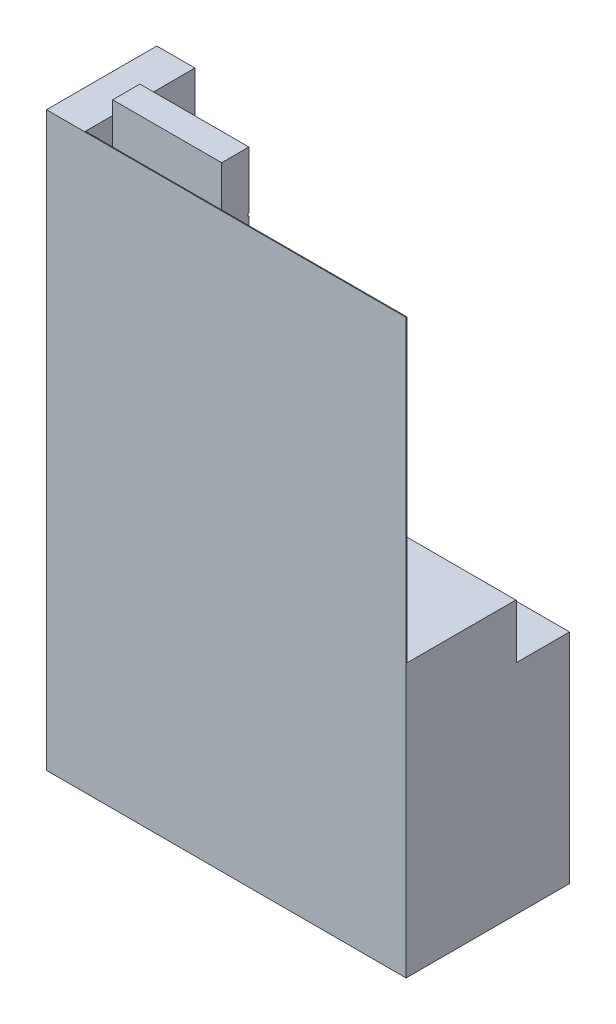
SolidWorks part; units mm, degrees
material "Balsa"
ref_plane "Front Plane" through (0, 0, 0) normal (0, 0, 1) x (1, 0, 0)
ref_plane "Top Plane" through (0, 0, 0) normal (0, 1, 0) x (1, 0, 0)
ref_plane "Right Plane" through (0, 0, 0) normal (1, 0, 0) x (0, 0, -1)
sketch "Sketch1" plane through (0, 0, 0) normal (0, 0, 1) x (1, 0, 0)
  line L1 (-600, 400) -> (600, 400)
  line L2 (-600, 400) -> (-600, -400)
  line L3 (-600, -400) -> (600, -400)
  line L4 (600, 400) -> (600, -400)
  line L5 (-600, 400) -> (600, -400) construction
  line L6 (-600, -400) -> (600, 400) construction
  point P0 (0, 0)
  dimension "D1" = 1200
  dimension "D2" = 800
extrude "Boss-Extrude1" add sketch "Sketch1" along normal blind 600
sketch "Sketch2" plane through (0, 0, 600) normal (0, 0, 1) x (1, 0, 0)
  line L0 (-600, -400) -> (600, -400) construction
  line L1 (600, 400) -> (-600, 400)
  line L2 (600, 400) -> (600, 1700)
  line L3 (600, 1700) -> (-600, 1700)
  line L4 (-600, 400) -> (-600, 1700)
  dimension "D1" = 2100
extrude "Boss-Extrude2" add sketch "Sketch2" against normal blind 3
sketch "Sketch5" plane through (0, 0, 597) normal (0, 0, -1) x (-1, 0, 0)
  line L0 (600, 1700) -> (600, 400) construction
  line L1 (600, 600) -> (-600, 600)
  line L2 (600, 600) -> (600, 590)
  line L3 (600, 590) -> (-600, 590)
  line L4 (-600, 600) -> (-600, 590)
  line L5 (600, 400) -> (-600, 400) construction
  dimension "D1" = 10
  dimension "D2" = 1200
  dimension "D3" = 190
extrude "Boss-Extrude6" add sketch "Sketch5" along normal blind 400
sketch "Sketch11" plane through (0, 0, 0) normal (1, 0, 0) x (0, 0, -1)
  line L0 (-197, 600) -> (0, 400)
rib "Rib1" sketch "Sketch11" sketch "Sketch11" thickness 1200 extrusion direction parallel to sketch draft on no parameters "D1"=1200
sketch "Sketch12" plane through (-600, 0, 0) normal (-1, 0, 0) x (0, 0, 1)
  line L0 (0, 400) -> (-7.2932, 406.8417)
  dimension "D1" = 10
extrude "Extrude-Thin1" add sketch "Sketch12" against normal up to surface (1200 mm away) thin
sketch "Sketch16" plane through (0, 0, 597) normal (0, 0, -1) x (-1, 0, 0)
  line L0 (600, 1700) -> (600, 600) construction
  line L1 (600, 927) -> (0, 927)
  line L2 (600, 927) -> (600, 917)
  line L3 (600, 917) -> (0, 917)
  line L4 (0, 927) -> (0, 917)
  line L5 (600, 600) -> (-600, 600) construction
  dimension "D1" = 317
  dimension "D2" = 10
  dimension "D3" = 600
extrude "Boss-Extrude11" add sketch "Sketch16" along normal blind 375
sketch "Sketch17" plane through (0, 0, 597) normal (0, 0, -1) x (-1, 0, 0)
  line L0 (600, 1700) -> (600, 927) construction
  line L1 (600, 1287) -> (0, 1287)
  line L2 (600, 1287) -> (600, 1277)
  line L3 (600, 1277) -> (0, 1277)
  line L4 (0, 1287) -> (0, 1277)
  line L5 (600, 927) -> (0, 927) construction
  dimension "D1" = 10
  dimension "D2" = 350
  dimension "D3" = 600
extrude "Boss-Extrude12" add sketch "Sketch17" along normal blind 375
sketch "Sketch18" plane through (0, 0, 597) normal (0, 0, -1) x (-1, 0, 0)
  line L1 (-513.7917, 1599.2738) -> (-63.7917, 1599.2738)
  line L2 (-513.7917, 1599.2738) -> (-513.7917, 849.2738)
  line L3 (-513.7917, 849.2738) -> (-63.7917, 849.2738)
  line L4 (-63.7917, 1599.2738) -> (-63.7917, 849.2738)
  dimension "D1" = 450
  dimension "D2" = 750
extrude "Boss-Extrude13" add sketch "Sketch18" along normal blind 40 separate body
sketch "Sketch21" plane through (0, 0, 557) normal (0, 0, -1) x (-1, 0, 0)
  line L0 (-513.7917, 1599.2738) -> (-513.7917, 849.2738) construction
  text T0 "Back Light" font "BodoniFLF" height in points 200
  point P3 (-513.7917, 1224.2738)
extrude "Cut-Extrude7" cut sketch "Sketch21" against normal blind 3
sketch "Sketch22" plane through (0, 0, 597) normal (0, 0, -1) x (-1, 0, 0)
  line L1 (100, 1850) -> (500, 1850)
  line L2 (100, 1850) -> (100, 1550)
  line L3 (100, 1550) -> (500, 1550)
  line L4 (500, 1850) -> (500, 1550)
  line L5 (-600, 1700) -> (600, 1700) construction
  line L6 (600, 1700) -> (600, 1287) construction
  point P6 (100, 1700)
  dimension "D1" = 400
  dimension "D2" = 300
  dimension "D3" = 100
extrude "Boss-Extrude15" add sketch "Sketch22" along normal blind 100 separate body
sketch "Sketch23" plane through (0, 0, 497) normal (0, 0, -1) x (-1, 0, 0)
  line L0 (100, 1850) -> (100, 1550) construction
  text T0 "ara" font "BodoniFLF" height in points 500
  text T1 "PERFUME" font "BodoniFLF" height in points 100
  point P3 (100, 1700)
  dimension "D1" = 60
  dimension "D2" = 80
  dimension "D3" = 47
extrude "Cut-Extrude10" cut sketch "Sketch23" against normal blind 3
sketch "Sketch24" plane through (0, 0, 497) normal (0, 0, -1) x (-1, 0, 0)
  line L0 (100, 1850) -> (100, 1550) construction
  line L1 (100, 1640) -> (185, 1640)
  line L2 (100, 1640) -> (100, 1630)
  line L3 (100, 1630) -> (185, 1630)
  line L4 (185, 1640) -> (185, 1630)
  line L5 (100, 1550) -> (500, 1550) construction
  line L6 (300, 1550) -> (300, 1609.9434) construction
  line L7 (500, 1630) -> (415, 1630)
  line L8 (415, 1640) -> (415, 1630)
  line L9 (500, 1640) -> (415, 1640)
  line L10 (500, 1640) -> (500, 1630)
  dimension "D1" = 85
  dimension "D2" = 80
  dimension "D3" = 10
extrude "Cut-Extrude11" cut sketch "Sketch24" against normal blind 3
sketch "Sketch27" plane through (0, 0, 600) normal (0, 0, 1) x (1, 0, 0)
  line L1 (-600, -400) -> (-740, -400)
  line L2 (-600, -400) -> (-600, 1700)
  line L3 (-600, 1700) -> (-740, 1700)
  line L4 (-740, -400) -> (-740, 1700)
  dimension "D1" = 140
extrude "Boss-Extrude17" add sketch "Sketch27" against normal blind 405
sketch "Sketch41" plane through (0, 194.0783, -206.8855) normal (0, 0.6842, -0.7293) x (-1, 0, 0)
  line L1 (-600, 300.7561) -> (600, 300.7561)
  line L2 (-600, 300.7561) -> (-600, 291.7282)
  line L3 (-600, 291.7282) -> (600, 291.7282)
  line L4 (600, 300.7561) -> (600, 291.7282)
extrude "Cut-Extrude17" cut sketch "Sketch41" against normal up to surface (10 mm away) up to face at (0, 403.2921, 3.0883)
sketch "Sketch45" plane through (0, 0, 195) normal (0, 0, -1) x (-1, 0, 0)
  line L1 (600, 400) -> (740, 400)
  line L2 (600, 400) -> (600, -400)
  line L3 (600, -400) -> (740, -400)
  line L4 (740, 400) -> (740, -400)
extrude "Boss-Extrude18" add sketch "Sketch45" along normal up to surface (195 mm away) up to face at (0, 0, 0)
sketch "Sketch46" plane through (-600, 0, 0) normal (-1, 0, 0) x (0, 0, 1)
  line L0 (0, 400) -> (195, 597.9695)
  line L1 (195, 597.9695) -> (195, 400)
  line L2 (195, 400) -> (0, 400)
extrude "Cut-Extrude21" cut sketch "Sketch46" against normal up to surface (1200 mm away) up to face at (600, 600, 370.1429)
sketch "Sketch47" plane through (0, 0, 0) normal (0, 0, -1) x (-1, 0, 0)
  line L0 (740, -400) -> (-600, -400) construction
  line L1 (-600, 1700) -> (-580, 1700)
  line L2 (-600, 1700) -> (-600, -400)
  line L3 (-600, -400) -> (-580, -400)
  line L4 (-580, 1700) -> (-580, -400)
  dimension "D1" = 20
extrude "Cut-Extrude22" cut sketch "Sketch47" against normal through all both and the other way through all
sketch "Sketch50" plane through (0, 0, 0) normal (0, 0, -1) x (-1, 0, 0)
  line L0 (740, -400) -> (-580, -400) construction
  line L1 (5, 400) -> (15, 400)
  line L2 (5, 400) -> (5, -400)
  line L3 (5, -400) -> (15, -400)
  line L4 (15, 400) -> (15, -400)
  line L5 (-580, 400) -> (740, 400) construction
  line L6 (-580, 400) -> (-580, -400) construction
  point P4 (53.5369, 358.9061)
  point P5 (124.1051, -400)
  point P8 (154.9787, 400)
  dimension "D1" = 10
  dimension "D2" = 585
extrude "Cut-Extrude23" cut sketch "Sketch50" against normal blind 10
sketch "Sketch52" plane through (0, 0, 0) normal (0, 0, -1) x (-1, 0, 0)
  line L0 (15, 400) -> (740, 400) construction
  line L1 (740, -400) -> (15, -400) construction
  line L2 (610, 400) -> (600, 400)
  line L3 (610, 400) -> (610, -400)
  line L4 (610, -400) -> (600, -400)
  line L5 (600, 400) -> (600, -400)
  line L6 (15, -400) -> (15, 400) construction
  dimension "D1" = 10
  dimension "D2" = 585
extrude "Cut-Extrude24" cut sketch "Sketch52" against normal blind 10
sketch "Sketch53" plane through (0, 0, 0) normal (0, 0, -1) x (-1, 0, 0)
  line L0 (15, -400) -> (15, 400) construction
  line L1 (600, 400) -> (600, -400) construction
  line L2 (740, 400) -> (-580, 400) construction
  circle A0 centre (307.5, 0) radius 15
  circle A1 centre (-277.5, 0) radius 15
  dimension "D1" = 30
  dimension "D2" = 292.5
  dimension "D3" = 400
extrude "Boss-Extrude19" add sketch "Sketch53" along normal blind 20
